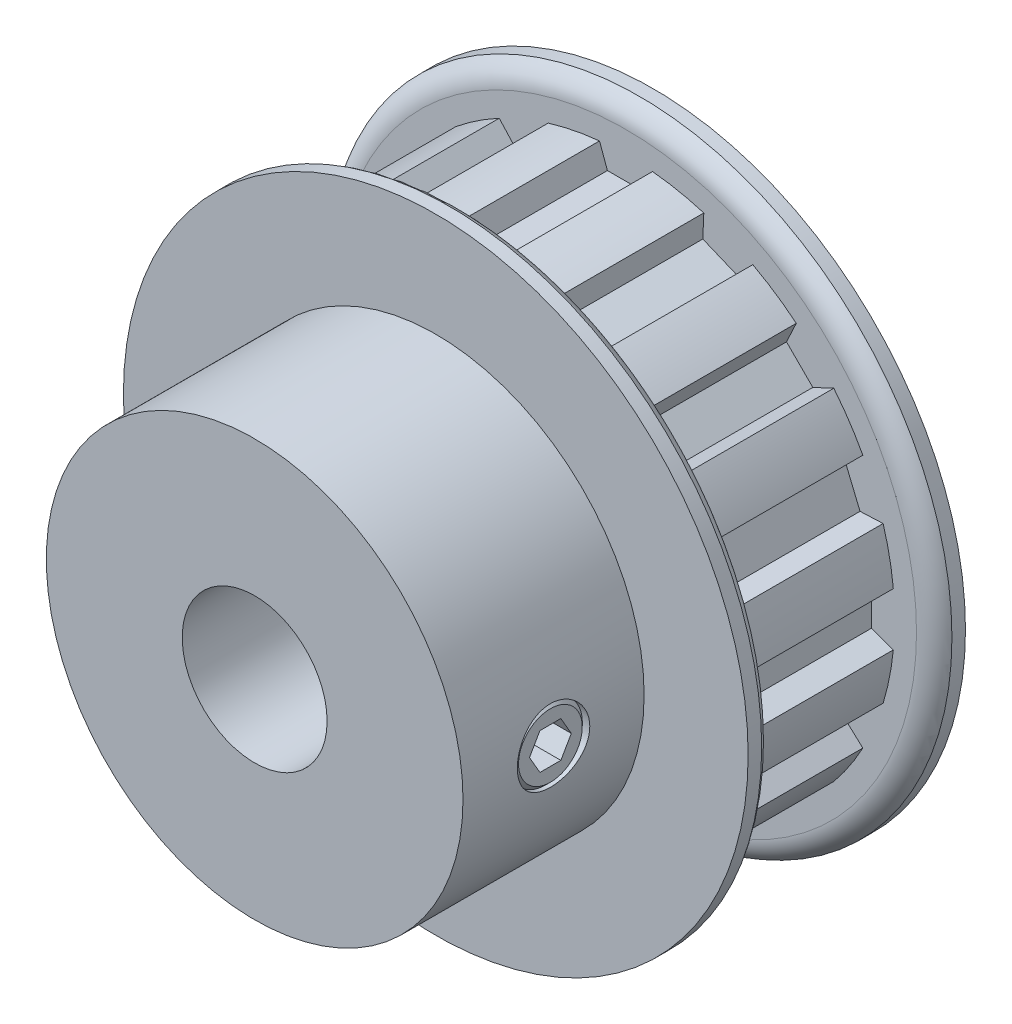
SolidWorks part; units mm, degrees
ref_plane "Front Plane" through (0, 0, 0) normal (0, 0, 1) x (1, 0, 0)
ref_plane "Top Plane" through (0, 0, 0) normal (0, 1, 0) x (1, 0, 0)
ref_plane "Right Plane" through (0, 0, 0) normal (1, 0, 0) x (0, 0, -1)
sketch "Sketch1" plane through (0, 0, 0) normal (0, 0, 1) x (1, 0, 0)
  line L0 (-2.3241, 23.4315) -> (-1.6307, 21.5265)
  line L1 (-1.6307, 21.5265) -> (1.6307, 21.5265)
  line L2 (1.6307, 21.5265) -> (2.3241, 23.4315)
  line L3 (-2.3241, 23.4315) -> (2.3241, 23.4315)
  line L4 (0, 0) -> (0, 21.5265) construction
  line L5 (0, 21.5265) -> (0, 25.0825) construction
  circle A0 centre (0, 0) radius 24.257 construction
  circle A1 centre (0, 0) radius 27.3812 construction
  circle A2 centre (0, 0) radius 23.5465 construction
  point P6 (0, 23.4315)
  point P11 (0, 24.257)
  point P13 (0, 27.3812)
  point P14 (0, 23.5465)
  dimension "D1" = 1.651
  dimension "PD" = 48.514
  dimension "D2" = 0.8255
  dimension "OD" = 54.7624
  dimension "b" = 40
  dimension "bt" = 4.6482
  dimension "ht" = 1.905
  dimension "hs" = 3.556
sketch "Sketch2" plane through (0, 0, 0) normal (1, 0, 0) x (0, 0, -1)
  line L0 (-17.4625, 6.35) -> (17.4625, 6.35)
  line L1 (-17.4625, 6.35) -> (-17.4625, 18.2626)
  line L2 (-17.4625, 18.2626) -> (-1.5875, 18.2626)
  line L3 (-1.5875, 18.2626) -> (-1.5875, 27.3812)
  line L4 (-1.5875, 27.3812) -> (0.7874, 27.3812) construction
  line L5 (0.7874, 27.3812) -> (0.7874, 23.5465) construction
  line L6 (0.7874, 23.5465) -> (15.0876, 23.5465)
  line L7 (15.0876, 23.5465) -> (15.0876, 27.3812) construction
  line L8 (15.0876, 27.3812) -> (17.4625, 27.3812) construction
  line L9 (17.4625, 27.3812) -> (17.4625, 6.35)
  line L10 (-17.4625, 0) -> (17.4625, 0) construction
  line L13 (-1.5875, 27.3812) -> (-0.4001, 27.3812)
  line L14 (0.7874, 25.4638) -> (0.7874, 23.5465)
  line L15 (15.0876, 23.5465) -> (15.0876, 25.4638)
  line L16 (16.2751, 27.3812) -> (17.4625, 27.3812)
  arc A0 (0.7874, 25.4638) -> (-0.4001, 27.3812) centre (-1.3543, 25.4638) ccw
  arc A1 (15.0876, 25.4638) -> (16.2751, 27.3812) centre (17.2293, 25.4638) cw
  point P12 (0.7874, 25.4638)
  point P14 (-0.4001, 27.3812)
  point P20 (15.0876, 25.4638)
  point P21 (16.2751, 27.3812)
  point P25 (15.0876, 0)
  point P26 (0.7874, 0)
  dimension "OA" = 34.925
  dimension "Bore" = 12.7
  dimension "Hub Dia" = 36.5252
  dimension "Outside Width" = 19.05
  dimension "Inside Width" = 14.3002
revolve "Revolve1" add sketch "Sketch2" angle 360 mid plane about L10
sketch "Sketch3" plane through (0, 0, 0) normal (0, 0, 1) x (1, 0, 0)
  line L0 (-1.6307, 21.5265) -> (1.6307, 21.5265) construction
  line L1 (1.6307, 21.5265) -> (2.3241, 23.4315) construction
  line L2 (-2.3241, 23.4315) -> (-1.6307, 21.5265) construction
  line L3 (-1.6307, 21.5265) -> (1.6307, 21.5265)
  line L4 (1.6307, 21.5265) -> (2.3241, 23.4315)
  line L5 (-2.3241, 23.4315) -> (-1.6307, 21.5265)
  circle A0 centre (0, 0) radius 23.5465 construction
  arc A1 (2.3241, 23.4315) -> (-2.3241, 23.4315) centre (0, 0) ccw
extrude "Cut-Extrude1" cut sketch "Sketch3" against normal up to vertex (15.0876 mm away) from vertex at -0.7874 starting at point (0, 23.5465, -0.7874)
pattern_circular "CirPattern1" count 16 over 360 about axis through (0, 0, 0) along (0, 0, 1) of "Cut-Extrude1"
sketch "Sketch4" plane through (0, 0, 0) normal (1, 0, 0) x (0, -1, 0)
  line L0 (0, -1.5875) -> (0, -17.4625) construction
  line L1 (-18.2626, -1.5875) -> (18.2626, -1.5875) construction
  line L2 (-18.2626, -17.4625) -> (18.2626, -17.4625) construction
  circle A0 centre (0, -9.525) radius 3.175
  dimension "D1" = 6.35
extrude "Cut-Extrude2" cut sketch "Sketch4" along normal through all
ref_plane "Plane1" through (0, 0, 9.525) normal (0, 0, 1) x (1, 0, 0)
sketch "Sketch5" plane through (0, 0, 9.525) normal (0, 0, 1) x (1, 0, 0)
  line L0 (0, 0.1664) -> (0, 18.2626) construction
  line L1 (6.35, -2.794) -> (6.35, 0)
  line L2 (6.731, -3.175) -> (17.6035, -3.175)
  line L3 (6.35, 0) -> (18.2626, 0) construction
  line L4 (6.35, 0) -> (17.9845, 0)
  line L5 (17.9845, 0) -> (17.9845, -2.794)
  line L6 (6.731, -3.175) -> (6.35, -2.794)
  line L7 (17.9845, -2.794) -> (17.6035, -3.175)
  circle A0 centre (0, 0) radius 18.2626 construction
  circle A1 centre (0, 0) radius 6.35 construction
  point P2 (6.35, -3.175)
  point P11 (17.9845, -3.175)
revolve "Revolve2" add sketch "Sketch5" angle 360 mid plane about L4
sketch "Sketch6" plane through (17.9845, 5.3841, 0) normal (-1, 0, 0) x (0, -1, 0)
  line L1 (5.3841, 11.3581) -> (3.7966, 10.4415)
  line L2 (3.7966, 10.4415) -> (3.7966, 8.6085)
  line L3 (3.7966, 8.6085) -> (5.3841, 7.6919)
  line L4 (5.3841, 7.6919) -> (6.9716, 8.6085)
  line L5 (6.9716, 8.6085) -> (6.9716, 10.4415)
  line L6 (6.9716, 10.4415) -> (5.3841, 11.3581)
  circle A0 centre (5.3841, 9.525) radius 1.5875 construction
  dimension "D1" = 3.175
extrude "Cut-Extrude3" cut sketch "Sketch6" along normal blind 2.3813
equation "\"D2@Sketch1\" = \"D1@Sketch1\"/2"
equation "\"D1@Sketch4\" = \"Bore@Sketch2\"/2"
equation "\"D1@Sketch6\" = \"D1@Sketch4\"/2"
equation "\"D1@Cut-Extrude3\" = \"D1@Sketch6\"*.75"
